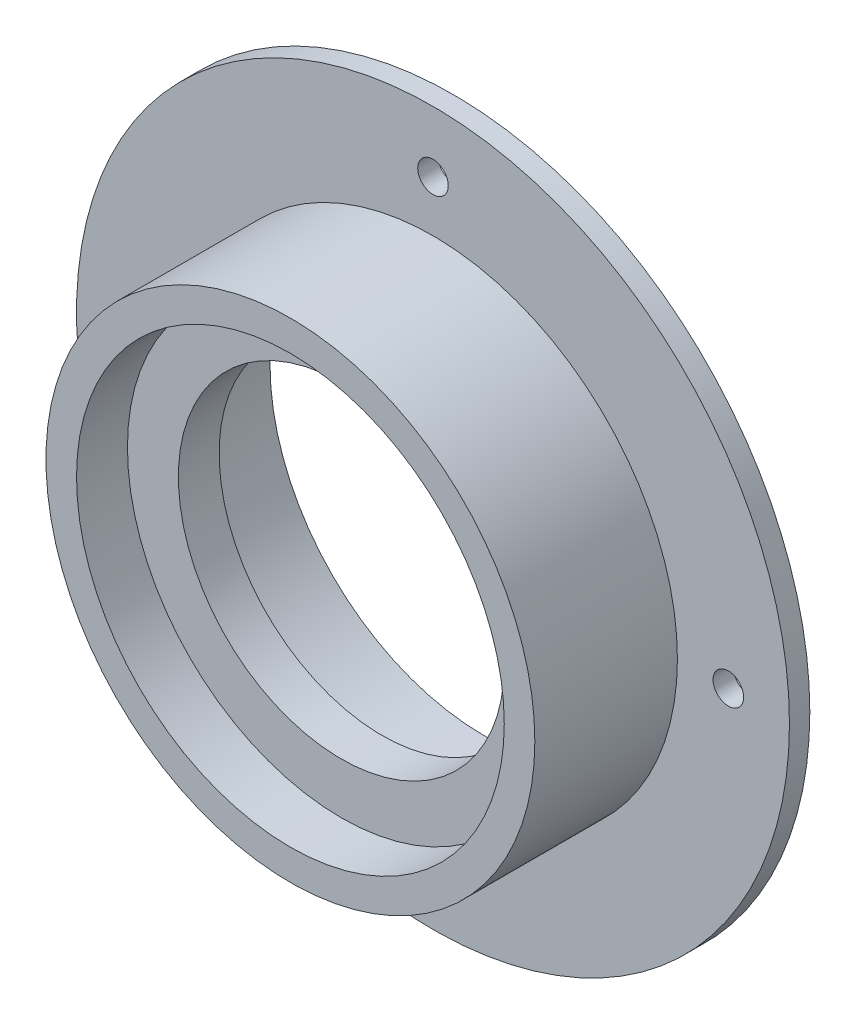
SolidWorks part; units mm, degrees
material "Alloy Steel (SS)"
ref_plane "Front Plane" through (0, 0, 0) normal (0, 0, 1) x (1, 0, 0)
ref_plane "Top Plane" through (0, 0, 0) normal (0, 1, 0) x (1, 0, 0)
ref_plane "Right Plane" through (0, 0, 0) normal (1, 0, 0) x (0, 0, -1)
sketch "Sketch1" plane through (0, 0, 0) normal (0, 0, 1) x (1, 0, 0)
  circle A0 centre (0, 0) radius 35
  dimension "D1" = 70
extrude "Boss-Extrude1" add sketch "Sketch1" along normal blind 2
sketch "Sketch2" plane through (0, 0, 2) normal (0, 0, 1) x (1, 0, 0)
  circle A0 centre (0, 0) radius 24
  circle A1 centre (0, 0) radius 21
  dimension "D1" = 48
  dimension "D2" = 42
extrude "Boss-Extrude2" add sketch "Sketch2" along normal blind 14
sketch "Sketch3" plane through (0, 0, 2) normal (0, 0, 1) x (1, 0, 0)
  circle A0 centre (0, 0) radius 21
extrude "Cut-Extrude1" cut sketch "Sketch3" against normal blind 10
sketch "Sketch4" plane through (0, 0, 0) normal (0, 0, -1) x (-1, 0, 0)
  circle A0 centre (0, 0) radius 29 construction
  circle A1 centre (29, 0) radius 1.5
  circle A2 centre (0, -29) radius 1.5
  circle A3 centre (-29, 0) radius 1.5
  circle A4 centre (0, 29) radius 1.5
  dimension "D1" = 58
  dimension "D2" = 3
  dimension "D3" = 4
extrude "Cut-Extrude2" cut sketch "Sketch4" against normal up to next
sketch "Sketch5" plane through (0, 0, 16) normal (0, 0, 1) x (1, 0, 0)
  circle A0 centre (0, 0) radius 16
  circle A1 centre (0, 0) radius 21 construction
  circle A2 centre (0, 0) radius 21
  dimension "D1" = 5
extrude "Boss-Extrude3" add sketch "Sketch5" against normal blind 4 from offset 5 offset against normal yes
sketch "Sketch6" plane through (0, 0, 0) normal (0, 0, -1) x (-1, 0, 0)
  circle A2 centre (0, 0) radius 21
  circle A3 centre (0, 0) radius 21
  circle A4 centre (0, 0) radius 24
  circle A5 centre (0, 0) radius 24
  dimension "D1" = 0
  dimension "D2" = 0
extrude "Boss-Extrude4" add sketch "Sketch6" along normal blind 3
